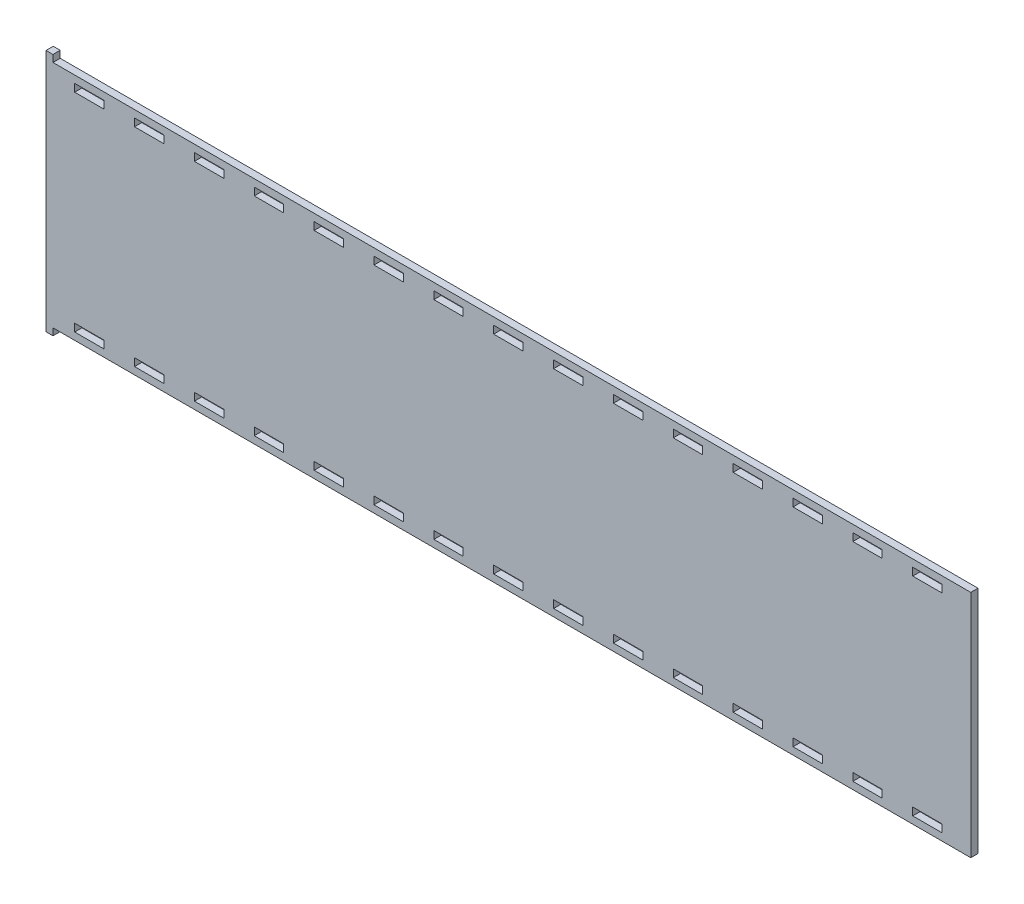
SolidWorks part; units mm, degrees
ref_plane "Front Plane" through (0, 0, 0) normal (0, 0, 1) x (1, 0, 0)
ref_plane "Top Plane" through (0, 0, 0) normal (0, 1, 0) x (1, 0, 0)
ref_plane "Right Plane" through (0, 0, 0) normal (1, 0, 0) x (0, 0, -1)
sketch "Sketch1" plane through (0, 0, 0) normal (0, 0, 1) x (1, 0, 0)
  line L8 (25.5, 94.5404) -> (12.6, 94.5404)
  line L9 (25.5, 91.1622) -> (25.5, 94.5404)
  line L10 (12.6, 91.1622) -> (25.5, 91.1622)
  line L11 (12.6, 94.5404) -> (12.6, 91.1622)
  line L16 (51.8071, 94.5404) -> (38.9071, 94.5404)
  line L17 (51.8071, 91.1622) -> (51.8071, 94.5404)
  line L18 (38.9071, 91.1622) -> (51.8071, 91.1622)
  line L19 (38.9071, 94.5404) -> (38.9071, 91.1622)
  line L24 (393.8, 94.5404) -> (380.9, 94.5404)
  line L25 (393.8, 91.1622) -> (393.8, 94.5404)
  line L26 (380.9, 91.1622) -> (393.8, 91.1622)
  line L27 (380.9, 94.5404) -> (380.9, 91.1622)
  line L32 (367.4929, 94.5404) -> (354.5929, 94.5404)
  line L33 (367.4929, 91.1622) -> (367.4929, 94.5404)
  line L34 (354.5929, 91.1622) -> (367.4929, 91.1622)
  line L35 (354.5929, 94.5404) -> (354.5929, 91.1622)
  line L40 (78.1143, 94.5404) -> (65.2143, 94.5404)
  line L41 (78.1143, 91.1622) -> (78.1143, 94.5404)
  line L42 (65.2143, 91.1622) -> (78.1143, 91.1622)
  line L43 (65.2143, 94.5404) -> (65.2143, 91.1622)
  line L48 (104.4214, 94.5404) -> (91.5214, 94.5404)
  line L49 (104.4214, 91.1622) -> (104.4214, 94.5404)
  line L50 (91.5214, 91.1622) -> (104.4214, 91.1622)
  line L51 (91.5214, 94.5404) -> (91.5214, 91.1622)
  line L56 (130.7286, 94.5404) -> (117.8286, 94.5404)
  line L57 (130.7286, 91.1622) -> (130.7286, 94.5404)
  line L58 (117.8286, 91.1622) -> (130.7286, 91.1622)
  line L59 (117.8286, 94.5404) -> (117.8286, 91.1622)
  line L64 (157.0357, 94.5404) -> (144.1357, 94.5404)
  line L65 (157.0357, 91.1622) -> (157.0357, 94.5404)
  line L66 (144.1357, 91.1622) -> (157.0357, 91.1622)
  line L67 (144.1357, 94.5404) -> (144.1357, 91.1622)
  line L72 (183.3429, 94.5404) -> (170.4429, 94.5404)
  line L73 (183.3429, 91.1622) -> (183.3429, 94.5404)
  line L74 (170.4429, 91.1622) -> (183.3429, 91.1622)
  line L75 (170.4429, 94.5404) -> (170.4429, 91.1622)
  line L80 (209.65, 94.5404) -> (196.75, 94.5404)
  line L81 (209.65, 91.1622) -> (209.65, 94.5404)
  line L82 (196.75, 91.1622) -> (209.65, 91.1622)
  line L83 (196.75, 94.5404) -> (196.75, 91.1622)
  line L88 (235.9571, 94.5404) -> (223.0571, 94.5404)
  line L89 (235.9571, 91.1622) -> (235.9571, 94.5404)
  line L90 (223.0571, 91.1622) -> (235.9571, 91.1622)
  line L91 (223.0571, 94.5404) -> (223.0571, 91.1622)
  line L96 (262.2643, 94.5404) -> (249.3643, 94.5404)
  line L97 (262.2643, 91.1622) -> (262.2643, 94.5404)
  line L98 (249.3643, 91.1622) -> (262.2643, 91.1622)
  line L99 (249.3643, 94.5404) -> (249.3643, 91.1622)
  line L104 (288.5714, 94.5404) -> (275.6714, 94.5404)
  line L105 (288.5714, 91.1622) -> (288.5714, 94.5404)
  line L106 (275.6714, 91.1622) -> (288.5714, 91.1622)
  line L107 (275.6714, 94.5404) -> (275.6714, 91.1622)
  line L112 (314.8786, 94.5404) -> (301.9786, 94.5404)
  line L113 (314.8786, 91.1622) -> (314.8786, 94.5404)
  line L114 (301.9786, 91.1622) -> (314.8786, 91.1622)
  line L115 (301.9786, 94.5404) -> (301.9786, 91.1622)
  line L120 (341.1857, 94.5404) -> (328.2857, 94.5404)
  line L121 (341.1857, 91.1622) -> (341.1857, 94.5404)
  line L122 (328.2857, 91.1622) -> (341.1857, 91.1622)
  line L123 (328.2857, 94.5404) -> (328.2857, 91.1622)
  line L128 (380.9, -0.1032) -> (393.8, -0.1032)
  line L129 (380.9, 3.275) -> (380.9, -0.1032)
  line L130 (393.8, 3.275) -> (380.9, 3.275)
  line L131 (393.8, -0.1032) -> (393.8, 3.275)
  line L136 (354.5929, -0.1032) -> (367.4929, -0.1032)
  line L137 (354.5929, 3.275) -> (354.5929, -0.1032)
  line L138 (367.4929, 3.275) -> (354.5929, 3.275)
  line L139 (367.4929, -0.1032) -> (367.4929, 3.275)
  line L144 (328.2857, -0.1032) -> (341.1857, -0.1032)
  line L145 (328.2857, 3.275) -> (328.2857, -0.1032)
  line L146 (341.1857, 3.275) -> (328.2857, 3.275)
  line L147 (341.1857, -0.1032) -> (341.1857, 3.275)
  line L152 (301.9786, -0.1032) -> (314.8786, -0.1032)
  line L153 (301.9786, 3.275) -> (301.9786, -0.1032)
  line L154 (314.8786, 3.275) -> (301.9786, 3.275)
  line L155 (314.8786, -0.1032) -> (314.8786, 3.275)
  line L160 (275.6714, -0.1032) -> (288.5714, -0.1032)
  line L161 (275.6714, 3.275) -> (275.6714, -0.1032)
  line L162 (288.5714, 3.275) -> (275.6714, 3.275)
  line L163 (288.5714, -0.1032) -> (288.5714, 3.275)
  line L168 (249.3643, -0.1032) -> (262.2643, -0.1032)
  line L169 (249.3643, 3.275) -> (249.3643, -0.1032)
  line L170 (262.2643, 3.275) -> (249.3643, 3.275)
  line L171 (262.2643, -0.1032) -> (262.2643, 3.275)
  line L176 (223.0571, -0.1032) -> (235.9571, -0.1032)
  line L177 (223.0571, 3.275) -> (223.0571, -0.1032)
  line L178 (235.9571, 3.275) -> (223.0571, 3.275)
  line L179 (235.9571, -0.1032) -> (235.9571, 3.275)
  line L184 (196.75, -0.1032) -> (209.65, -0.1032)
  line L185 (196.75, 3.275) -> (196.75, -0.1032)
  line L186 (209.65, 3.275) -> (196.75, 3.275)
  line L187 (209.65, -0.1032) -> (209.65, 3.275)
  line L192 (170.4429, -0.1032) -> (183.3429, -0.1032)
  line L193 (170.4429, 3.275) -> (170.4429, -0.1032)
  line L194 (183.3429, 3.275) -> (170.4429, 3.275)
  line L195 (183.3429, -0.1032) -> (183.3429, 3.275)
  line L200 (144.1357, -0.1032) -> (157.0357, -0.1032)
  line L201 (144.1357, 3.275) -> (144.1357, -0.1032)
  line L202 (157.0357, 3.275) -> (144.1357, 3.275)
  line L203 (157.0357, -0.1032) -> (157.0357, 3.275)
  line L208 (117.8286, -0.1032) -> (130.7286, -0.1032)
  line L209 (117.8286, 3.275) -> (117.8286, -0.1032)
  line L210 (130.7286, 3.275) -> (117.8286, 3.275)
  line L211 (130.7286, -0.1032) -> (130.7286, 3.275)
  line L216 (91.5214, -0.1032) -> (104.4214, -0.1032)
  line L217 (91.5214, 3.275) -> (91.5214, -0.1032)
  line L218 (104.4214, 3.275) -> (91.5214, 3.275)
  line L219 (104.4214, -0.1032) -> (104.4214, 3.275)
  line L224 (65.2143, -0.1032) -> (78.1143, -0.1032)
  line L225 (65.2143, 3.275) -> (65.2143, -0.1032)
  line L226 (78.1143, 3.275) -> (65.2143, 3.275)
  line L227 (78.1143, -0.1032) -> (78.1143, 3.275)
  line L232 (38.9071, -0.1032) -> (51.8071, -0.1032)
  line L233 (38.9071, 3.275) -> (38.9071, -0.1032)
  line L234 (51.8071, 3.275) -> (38.9071, 3.275)
  line L235 (51.8071, -0.1032) -> (51.8071, 3.275)
  line L240 (12.6, -0.1032) -> (25.5, -0.1032)
  line L241 (12.6, 3.275) -> (12.6, -0.1032)
  line L242 (25.5, 3.275) -> (12.6, 3.275)
  line L243 (25.5, -0.1032) -> (25.5, 3.275)
  line L256 (3.0496, 100.7618) -> (0, 100.7618)
  line L257 (0, 100.7618) -> (0, -6.3246)
  line L258 (0, -6.3246) -> (3.0496, -6.3246)
  line L259 (3.0496, -6.3246) -> (3.0496, -3.2782)
  line L260 (3.0496, -3.2782) -> (406.4, -3.2782)
  line L261 (406.4, -3.2782) -> (406.4, 97.7154)
  line L262 (406.4, 97.7154) -> (3.0496, 97.7154)
  line L263 (3.0496, 97.7154) -> (3.0496, 100.7618)
extrude "Boss-Extrude1" add sketch "Sketch1" along normal blind 3.175
sketch "DXF" plane through (0, 0, 0) normal (0, 0, 1) x (1, 0, 0)
  line L0 (25.3984, 94.4388) -> (12.7016, 94.4388)
  line L1 (12.7016, 94.4388) -> (12.7016, 91.2638)
  line L2 (12.7016, 91.2638) -> (25.3984, 91.2638)
  line L3 (25.3984, 91.2638) -> (25.3984, 94.4388)
  line L4 (51.7055, 94.4388) -> (39.0087, 94.4388)
  line L5 (39.0087, 94.4388) -> (39.0087, 91.2638)
  line L6 (39.0087, 91.2638) -> (51.7055, 91.2638)
  line L7 (51.7055, 91.2638) -> (51.7055, 94.4388)
  line L8 (25.5, 94.5404) -> (12.6, 94.5404) construction
  line L9 (25.5, 91.1622) -> (25.5, 94.5404) construction
  line L10 (12.6, 91.1622) -> (25.5, 91.1622) construction
  line L11 (12.6, 94.5404) -> (12.6, 91.1622) construction
  line L12 (393.6984, 94.4388) -> (381.0016, 94.4388)
  line L13 (381.0016, 94.4388) -> (381.0016, 91.2638)
  line L14 (381.0016, 91.2638) -> (393.6984, 91.2638)
  line L15 (393.6984, 91.2638) -> (393.6984, 94.4388)
  line L16 (51.8071, 94.5404) -> (38.9071, 94.5404) construction
  line L17 (51.8071, 91.1622) -> (51.8071, 94.5404) construction
  line L18 (38.9071, 91.1622) -> (51.8071, 91.1622) construction
  line L19 (38.9071, 94.5404) -> (38.9071, 91.1622) construction
  line L20 (367.3913, 94.4388) -> (354.6945, 94.4388)
  line L21 (354.6945, 94.4388) -> (354.6945, 91.2638)
  line L22 (354.6945, 91.2638) -> (367.3913, 91.2638)
  line L23 (367.3913, 91.2638) -> (367.3913, 94.4388)
  line L24 (393.8, 94.5404) -> (380.9, 94.5404) construction
  line L25 (393.8, 91.1622) -> (393.8, 94.5404) construction
  line L26 (380.9, 91.1622) -> (393.8, 91.1622) construction
  line L27 (380.9, 94.5404) -> (380.9, 91.1622) construction
  line L28 (78.0127, 94.4388) -> (65.3159, 94.4388)
  line L29 (65.3159, 94.4388) -> (65.3159, 91.2638)
  line L30 (65.3159, 91.2638) -> (78.0127, 91.2638)
  line L31 (78.0127, 91.2638) -> (78.0127, 94.4388)
  line L32 (367.4929, 94.5404) -> (354.5929, 94.5404) construction
  line L33 (367.4929, 91.1622) -> (367.4929, 94.5404) construction
  line L34 (354.5929, 91.1622) -> (367.4929, 91.1622) construction
  line L35 (354.5929, 94.5404) -> (354.5929, 91.1622) construction
  line L36 (104.3198, 94.4388) -> (91.623, 94.4388)
  line L37 (91.623, 94.4388) -> (91.623, 91.2638)
  line L38 (91.623, 91.2638) -> (104.3198, 91.2638)
  line L39 (104.3198, 91.2638) -> (104.3198, 94.4388)
  line L40 (78.1143, 94.5404) -> (65.2143, 94.5404) construction
  line L41 (78.1143, 91.1622) -> (78.1143, 94.5404) construction
  line L42 (65.2143, 91.1622) -> (78.1143, 91.1622) construction
  line L43 (65.2143, 94.5404) -> (65.2143, 91.1622) construction
  line L44 (130.627, 94.4388) -> (117.9302, 94.4388)
  line L45 (117.9302, 94.4388) -> (117.9302, 91.2638)
  line L46 (117.9302, 91.2638) -> (130.627, 91.2638)
  line L47 (130.627, 91.2638) -> (130.627, 94.4388)
  line L48 (104.4214, 94.5404) -> (91.5214, 94.5404) construction
  line L49 (104.4214, 91.1622) -> (104.4214, 94.5404) construction
  line L50 (91.5214, 91.1622) -> (104.4214, 91.1622) construction
  line L51 (91.5214, 94.5404) -> (91.5214, 91.1622) construction
  line L52 (156.9341, 94.4388) -> (144.2373, 94.4388)
  line L53 (144.2373, 94.4388) -> (144.2373, 91.2638)
  line L54 (144.2373, 91.2638) -> (156.9341, 91.2638)
  line L55 (156.9341, 91.2638) -> (156.9341, 94.4388)
  line L56 (130.7286, 94.5404) -> (117.8286, 94.5404) construction
  line L57 (130.7286, 91.1622) -> (130.7286, 94.5404) construction
  line L58 (117.8286, 91.1622) -> (130.7286, 91.1622) construction
  line L59 (117.8286, 94.5404) -> (117.8286, 91.1622) construction
  line L60 (183.2413, 94.4388) -> (170.5445, 94.4388)
  line L61 (170.5445, 94.4388) -> (170.5445, 91.2638)
  line L62 (170.5445, 91.2638) -> (183.2413, 91.2638)
  line L63 (183.2413, 91.2638) -> (183.2413, 94.4388)
  line L64 (157.0357, 94.5404) -> (144.1357, 94.5404) construction
  line L65 (157.0357, 91.1622) -> (157.0357, 94.5404) construction
  line L66 (144.1357, 91.1622) -> (157.0357, 91.1622) construction
  line L67 (144.1357, 94.5404) -> (144.1357, 91.1622) construction
  line L68 (209.5484, 94.4388) -> (196.8516, 94.4388)
  line L69 (196.8516, 94.4388) -> (196.8516, 91.2638)
  line L70 (196.8516, 91.2638) -> (209.5484, 91.2638)
  line L71 (209.5484, 91.2638) -> (209.5484, 94.4388)
  line L72 (183.3429, 94.5404) -> (170.4429, 94.5404) construction
  line L73 (183.3429, 91.1622) -> (183.3429, 94.5404) construction
  line L74 (170.4429, 91.1622) -> (183.3429, 91.1622) construction
  line L75 (170.4429, 94.5404) -> (170.4429, 91.1622) construction
  line L76 (235.8555, 94.4388) -> (223.1587, 94.4388)
  line L77 (223.1587, 94.4388) -> (223.1587, 91.2638)
  line L78 (223.1587, 91.2638) -> (235.8555, 91.2638)
  line L79 (235.8555, 91.2638) -> (235.8555, 94.4388)
  line L80 (209.65, 94.5404) -> (196.75, 94.5404) construction
  line L81 (209.65, 91.1622) -> (209.65, 94.5404) construction
  line L82 (196.75, 91.1622) -> (209.65, 91.1622) construction
  line L83 (196.75, 94.5404) -> (196.75, 91.1622) construction
  line L84 (262.1627, 94.4388) -> (249.4659, 94.4388)
  line L85 (249.4659, 94.4388) -> (249.4659, 91.2638)
  line L86 (249.4659, 91.2638) -> (262.1627, 91.2638)
  line L87 (262.1627, 91.2638) -> (262.1627, 94.4388)
  line L88 (235.9571, 94.5404) -> (223.0571, 94.5404) construction
  line L89 (235.9571, 91.1622) -> (235.9571, 94.5404) construction
  line L90 (223.0571, 91.1622) -> (235.9571, 91.1622) construction
  line L91 (223.0571, 94.5404) -> (223.0571, 91.1622) construction
  line L92 (288.4698, 94.4388) -> (275.773, 94.4388)
  line L93 (275.773, 94.4388) -> (275.773, 91.2638)
  line L94 (275.773, 91.2638) -> (288.4698, 91.2638)
  line L95 (288.4698, 91.2638) -> (288.4698, 94.4388)
  line L96 (262.2643, 94.5404) -> (249.3643, 94.5404) construction
  line L97 (262.2643, 91.1622) -> (262.2643, 94.5404) construction
  line L98 (249.3643, 91.1622) -> (262.2643, 91.1622) construction
  line L99 (249.3643, 94.5404) -> (249.3643, 91.1622) construction
  line L100 (314.777, 94.4388) -> (302.0802, 94.4388)
  line L101 (302.0802, 94.4388) -> (302.0802, 91.2638)
  line L102 (302.0802, 91.2638) -> (314.777, 91.2638)
  line L103 (314.777, 91.2638) -> (314.777, 94.4388)
  line L104 (288.5714, 94.5404) -> (275.6714, 94.5404) construction
  line L105 (288.5714, 91.1622) -> (288.5714, 94.5404) construction
  line L106 (275.6714, 91.1622) -> (288.5714, 91.1622) construction
  line L107 (275.6714, 94.5404) -> (275.6714, 91.1622) construction
  line L108 (341.0841, 94.4388) -> (328.3873, 94.4388)
  line L109 (328.3873, 94.4388) -> (328.3873, 91.2638)
  line L110 (328.3873, 91.2638) -> (341.0841, 91.2638)
  line L111 (341.0841, 91.2638) -> (341.0841, 94.4388)
  line L112 (314.8786, 94.5404) -> (301.9786, 94.5404) construction
  line L113 (314.8786, 91.1622) -> (314.8786, 94.5404) construction
  line L114 (301.9786, 91.1622) -> (314.8786, 91.1622) construction
  line L115 (301.9786, 94.5404) -> (301.9786, 91.1622) construction
  line L116 (381.0016, -0.0016) -> (393.6984, -0.0016)
  line L117 (393.6984, -0.0016) -> (393.6984, 3.1734)
  line L118 (393.6984, 3.1734) -> (381.0016, 3.1734)
  line L119 (381.0016, 3.1734) -> (381.0016, -0.0016)
  line L120 (341.1857, 94.5404) -> (328.2857, 94.5404) construction
  line L121 (341.1857, 91.1622) -> (341.1857, 94.5404) construction
  line L122 (328.2857, 91.1622) -> (341.1857, 91.1622) construction
  line L123 (328.2857, 94.5404) -> (328.2857, 91.1622) construction
  line L124 (354.6945, -0.0016) -> (367.3913, -0.0016)
  line L125 (367.3913, -0.0016) -> (367.3913, 3.1734)
  line L126 (367.3913, 3.1734) -> (354.6945, 3.1734)
  line L127 (354.6945, 3.1734) -> (354.6945, -0.0016)
  line L128 (380.9, -0.1032) -> (393.8, -0.1032) construction
  line L129 (380.9, 3.275) -> (380.9, -0.1032) construction
  line L130 (393.8, 3.275) -> (380.9, 3.275) construction
  line L131 (393.8, -0.1032) -> (393.8, 3.275) construction
  line L132 (328.3873, -0.0016) -> (341.0841, -0.0016)
  line L133 (341.0841, -0.0016) -> (341.0841, 3.1734)
  line L134 (341.0841, 3.1734) -> (328.3873, 3.1734)
  line L135 (328.3873, 3.1734) -> (328.3873, -0.0016)
  line L136 (354.5929, -0.1032) -> (367.4929, -0.1032) construction
  line L137 (354.5929, 3.275) -> (354.5929, -0.1032) construction
  line L138 (367.4929, 3.275) -> (354.5929, 3.275) construction
  line L139 (367.4929, -0.1032) -> (367.4929, 3.275) construction
  line L140 (302.0802, -0.0016) -> (314.777, -0.0016)
  line L141 (314.777, -0.0016) -> (314.777, 3.1734)
  line L142 (314.777, 3.1734) -> (302.0802, 3.1734)
  line L143 (302.0802, 3.1734) -> (302.0802, -0.0016)
  line L144 (328.2857, -0.1032) -> (341.1857, -0.1032) construction
  line L145 (328.2857, 3.275) -> (328.2857, -0.1032) construction
  line L146 (341.1857, 3.275) -> (328.2857, 3.275) construction
  line L147 (341.1857, -0.1032) -> (341.1857, 3.275) construction
  line L148 (275.773, -0.0016) -> (288.4698, -0.0016)
  line L149 (288.4698, -0.0016) -> (288.4698, 3.1734)
  line L150 (288.4698, 3.1734) -> (275.773, 3.1734)
  line L151 (275.773, 3.1734) -> (275.773, -0.0016)
  line L152 (301.9786, -0.1032) -> (314.8786, -0.1032) construction
  line L153 (301.9786, 3.275) -> (301.9786, -0.1032) construction
  line L154 (314.8786, 3.275) -> (301.9786, 3.275) construction
  line L155 (314.8786, -0.1032) -> (314.8786, 3.275) construction
  line L156 (249.4659, -0.0016) -> (262.1627, -0.0016)
  line L157 (262.1627, -0.0016) -> (262.1627, 3.1734)
  line L158 (262.1627, 3.1734) -> (249.4659, 3.1734)
  line L159 (249.4659, 3.1734) -> (249.4659, -0.0016)
  line L160 (275.6714, -0.1032) -> (288.5714, -0.1032) construction
  line L161 (275.6714, 3.275) -> (275.6714, -0.1032) construction
  line L162 (288.5714, 3.275) -> (275.6714, 3.275) construction
  line L163 (288.5714, -0.1032) -> (288.5714, 3.275) construction
  line L164 (223.1587, -0.0016) -> (235.8555, -0.0016)
  line L165 (235.8555, -0.0016) -> (235.8555, 3.1734)
  line L166 (235.8555, 3.1734) -> (223.1587, 3.1734)
  line L167 (223.1587, 3.1734) -> (223.1587, -0.0016)
  line L168 (249.3643, -0.1032) -> (262.2643, -0.1032) construction
  line L169 (249.3643, 3.275) -> (249.3643, -0.1032) construction
  line L170 (262.2643, 3.275) -> (249.3643, 3.275) construction
  line L171 (262.2643, -0.1032) -> (262.2643, 3.275) construction
  line L172 (196.8516, -0.0016) -> (209.5484, -0.0016)
  line L173 (209.5484, -0.0016) -> (209.5484, 3.1734)
  line L174 (209.5484, 3.1734) -> (196.8516, 3.1734)
  line L175 (196.8516, 3.1734) -> (196.8516, -0.0016)
  line L176 (223.0571, -0.1032) -> (235.9571, -0.1032) construction
  line L177 (223.0571, 3.275) -> (223.0571, -0.1032) construction
  line L178 (235.9571, 3.275) -> (223.0571, 3.275) construction
  line L179 (235.9571, -0.1032) -> (235.9571, 3.275) construction
  line L180 (170.5445, -0.0016) -> (183.2413, -0.0016)
  line L181 (183.2413, -0.0016) -> (183.2413, 3.1734)
  line L182 (183.2413, 3.1734) -> (170.5445, 3.1734)
  line L183 (170.5445, 3.1734) -> (170.5445, -0.0016)
  line L184 (196.75, -0.1032) -> (209.65, -0.1032) construction
  line L185 (196.75, 3.275) -> (196.75, -0.1032) construction
  line L186 (209.65, 3.275) -> (196.75, 3.275) construction
  line L187 (209.65, -0.1032) -> (209.65, 3.275) construction
  line L188 (144.2373, -0.0016) -> (156.9341, -0.0016)
  line L189 (156.9341, -0.0016) -> (156.9341, 3.1734)
  line L190 (156.9341, 3.1734) -> (144.2373, 3.1734)
  line L191 (144.2373, 3.1734) -> (144.2373, -0.0016)
  line L192 (170.4429, -0.1032) -> (183.3429, -0.1032) construction
  line L193 (170.4429, 3.275) -> (170.4429, -0.1032) construction
  line L194 (183.3429, 3.275) -> (170.4429, 3.275) construction
  line L195 (183.3429, -0.1032) -> (183.3429, 3.275) construction
  line L196 (117.9302, -0.0016) -> (130.627, -0.0016)
  line L197 (130.627, -0.0016) -> (130.627, 3.1734)
  line L198 (130.627, 3.1734) -> (117.9302, 3.1734)
  line L199 (117.9302, 3.1734) -> (117.9302, -0.0016)
  line L200 (144.1357, -0.1032) -> (157.0357, -0.1032) construction
  line L201 (144.1357, 3.275) -> (144.1357, -0.1032) construction
  line L202 (157.0357, 3.275) -> (144.1357, 3.275) construction
  line L203 (157.0357, -0.1032) -> (157.0357, 3.275) construction
  line L204 (91.623, -0.0016) -> (104.3198, -0.0016)
  line L205 (104.3198, -0.0016) -> (104.3198, 3.1734)
  line L206 (104.3198, 3.1734) -> (91.623, 3.1734)
  line L207 (91.623, 3.1734) -> (91.623, -0.0016)
  line L208 (117.8286, -0.1032) -> (130.7286, -0.1032) construction
  line L209 (117.8286, 3.275) -> (117.8286, -0.1032) construction
  line L210 (130.7286, 3.275) -> (117.8286, 3.275) construction
  line L211 (130.7286, -0.1032) -> (130.7286, 3.275) construction
  line L212 (65.3159, -0.0016) -> (78.0127, -0.0016)
  line L213 (78.0127, -0.0016) -> (78.0127, 3.1734)
  line L214 (78.0127, 3.1734) -> (65.3159, 3.1734)
  line L215 (65.3159, 3.1734) -> (65.3159, -0.0016)
  line L216 (91.5214, -0.1032) -> (104.4214, -0.1032) construction
  line L217 (91.5214, 3.275) -> (91.5214, -0.1032) construction
  line L218 (104.4214, 3.275) -> (91.5214, 3.275) construction
  line L219 (104.4214, -0.1032) -> (104.4214, 3.275) construction
  line L220 (39.0087, -0.0016) -> (51.7055, -0.0016)
  line L221 (51.7055, -0.0016) -> (51.7055, 3.1734)
  line L222 (51.7055, 3.1734) -> (39.0087, 3.1734)
  line L223 (39.0087, 3.1734) -> (39.0087, -0.0016)
  line L224 (65.2143, -0.1032) -> (78.1143, -0.1032) construction
  line L225 (65.2143, 3.275) -> (65.2143, -0.1032) construction
  line L226 (78.1143, 3.275) -> (65.2143, 3.275) construction
  line L227 (78.1143, -0.1032) -> (78.1143, 3.275) construction
  line L228 (12.7016, -0.0016) -> (25.3984, -0.0016)
  line L229 (25.3984, -0.0016) -> (25.3984, 3.1734)
  line L230 (25.3984, 3.1734) -> (12.7016, 3.1734)
  line L231 (12.7016, 3.1734) -> (12.7016, -0.0016)
  line L232 (38.9071, -0.1032) -> (51.8071, -0.1032) construction
  line L233 (38.9071, 3.275) -> (38.9071, -0.1032) construction
  line L234 (51.8071, 3.275) -> (38.9071, 3.275) construction
  line L235 (51.8071, -0.1032) -> (51.8071, 3.275) construction
  line L236 (-0.1016, 100.8634) -> (-0.1016, -6.4262)
  line L237 (-0.1016, -6.4262) -> (3.1512, -6.4262)
  line L238 (3.1512, -6.4262) -> (3.1512, -3.3798)
  line L239 (3.1512, -3.3798) -> (406.5016, -3.3798)
  line L240 (12.6, -0.1032) -> (25.5, -0.1032) construction
  line L241 (12.6, 3.275) -> (12.6, -0.1032) construction
  line L242 (25.5, 3.275) -> (12.6, 3.275) construction
  line L243 (25.5, -0.1032) -> (25.5, 3.275) construction
  line L244 (406.5016, -3.3798) -> (406.5016, 97.817)
  line L245 (406.5016, 97.817) -> (3.1512, 97.817)
  line L246 (3.1512, 97.817) -> (3.1512, 100.8634)
  line L247 (3.1512, 100.8634) -> (-0.1016, 100.8634)
  line L256 (3.0496, 100.7618) -> (0, 100.7618) construction
  line L257 (0, 100.7618) -> (0, -6.3246) construction
  line L258 (0, -6.3246) -> (3.0496, -6.3246) construction
  line L259 (3.0496, -6.3246) -> (3.0496, -3.2782) construction
  line L260 (3.0496, -3.2782) -> (406.4, -3.2782) construction
  line L261 (406.4, -3.2782) -> (406.4, 97.7154) construction
  line L262 (406.4, 97.7154) -> (3.0496, 97.7154) construction
  line L263 (3.0496, 97.7154) -> (3.0496, 100.7618) construction
  dimension "D1" = 0.1016
  dimension "D2" = 0.1016
extrude "DXF-Extrude" [suppressed] add sketch "DXF" along normal blind 3.175
